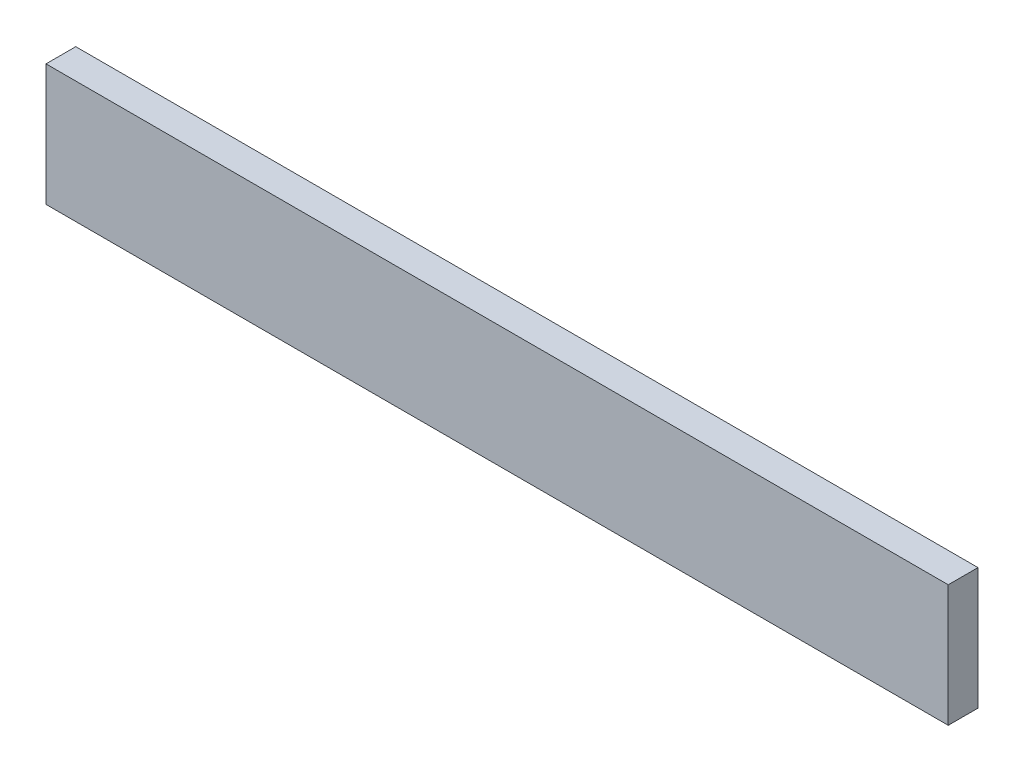
SolidWorks part; units mm, degrees
ref_plane "Face" through (0, 0, 0) normal (0, 0, 1) x (1, 0, 0)
ref_plane "Dessus" through (0, 0, 0) normal (0, 1, 0) x (1, 0, 0)
ref_plane "Droite" through (0, 0, 0) normal (1, 0, 0) x (0, 0, -1)
sketch "Esquisse1" plane through (0, 0, 0) normal (0, 0, 1) x (1, 0, 0)
  line L1 (0, 0) -> (667, 0)
  line L2 (0, 0) -> (0, 90)
  line L3 (0, 90) -> (667, 90)
  line L4 (667, 0) -> (667, 90)
  dimension "D1" = 667
  dimension "D2" = 90
extrude "Extrusion1" add sketch "Esquisse1" along normal blind 22
